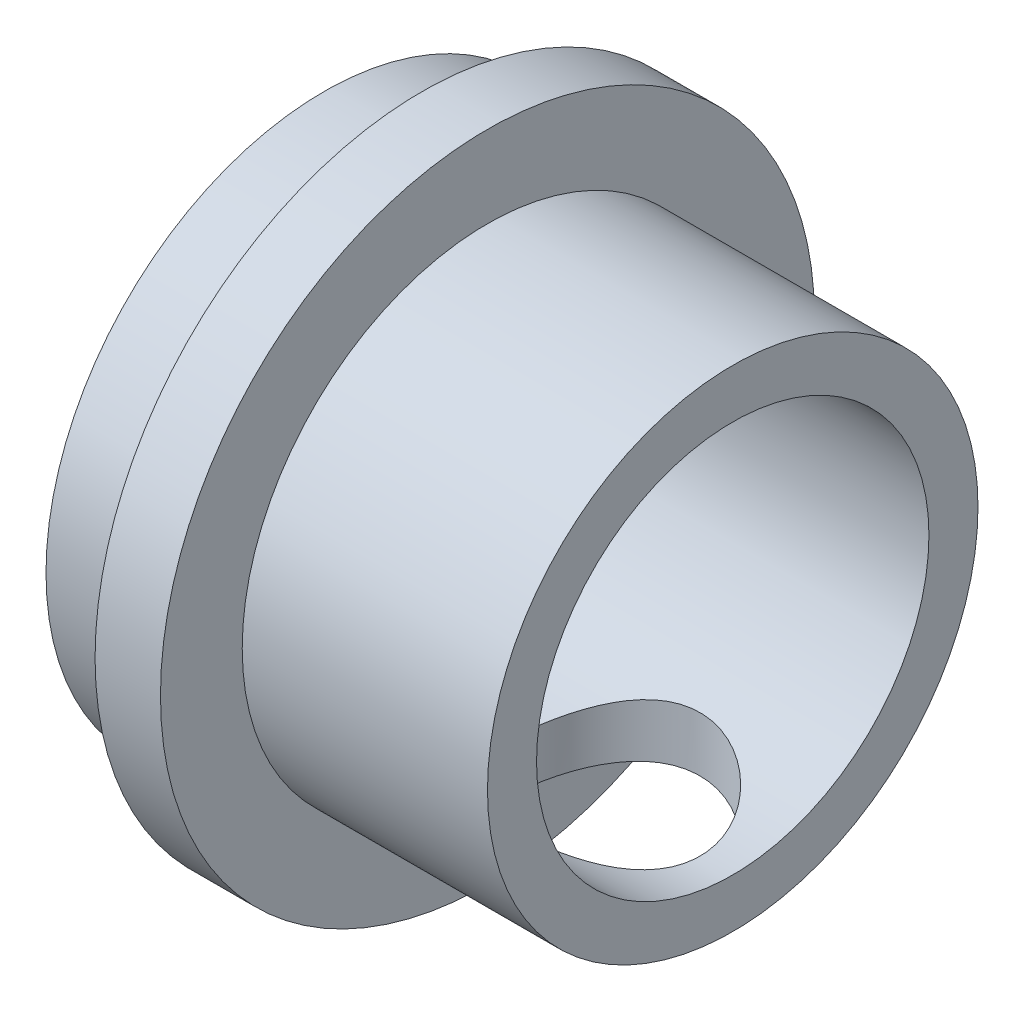
SolidWorks part; units mm, degrees
ref_plane "Face" through (0, 0, 0) normal (0, 0, 1) x (1, 0, 0)
ref_plane "Dessus" through (0, 0, 0) normal (0, 1, 0) x (1, 0, 0)
ref_plane "Droite" through (0, 0, 0) normal (1, 0, 0) x (0, 0, -1)
sketch "Esquisse1" plane through (0, 0, 0) normal (0, 0, 1) x (1, 0, 0)
  line L0 (-59.6035, 0) -> (58.8071, 0) construction
  line L1 (0, 0) -> (0, 8.5)
  line L2 (0, 8.5) -> (3, 8.5)
  line L3 (3, 8.5) -> (3, 9.0937)
  line L4 (3, 9.0937) -> (3, 10)
  line L5 (3, 10) -> (5, 10)
  line L6 (5, 10) -> (5, 7.5)
  line L7 (5, 7.5) -> (12.5, 7.5)
  line L8 (12.5, 7.5) -> (12.5, 0)
  line L9 (12.5, 0) -> (0, 0)
  dimension "D1" = 8.5
  dimension "D2" = 10
  dimension "D3" = 7.5
  dimension "D4" = 3
  dimension "D5" = 2
  dimension "D6" = 7.5
revolve "Révolution1" add sketch "Esquisse1" angle 360 about L0
sketch "Esquisse2" plane through (0, 0, 0) normal (-1, 0, 0) x (0, 0, 1)
  line L0 (-6.6668, 0) -> (7.051, 0) construction
  line L1 (0, 6.9357) -> (0, -4.6302) construction
  line L3 (-4, 4) -> (4, 4)
  line L4 (-4, 4) -> (-4, -4)
  line L5 (-4, -4) -> (4, -4)
  line L6 (4, 4) -> (4, -4)
  dimension "D1" = 8
  dimension "D2" = 8
extrude "Enlèv. mat.-Extru.1" cut sketch "Esquisse2" against normal through all
sketch "Esquisse3" plane through (12.5, 0, 0) normal (1, 0, 0) x (0, 0, -1)
  circle A0 centre (0, 0) radius 6
  dimension "D1" = 12
extrude "Enlèv. mat.-Extru.2" cut sketch "Esquisse3" against normal blind 10
sketch "Esquisse4" plane through (0, 0, 0) normal (0, 1, 0) x (1, 0, 0)
  line L0 (12.5, -7.5) -> (12.5, 7.5) construction
  line L2 (5, -7.5) -> (5, 7.5) construction
  circle A0 centre (8.5, 0) radius 3
  dimension "D1" = 6
  dimension "D2" = 4
  dimension "D3" = 3.5
extrude "Enlèv. mat.-Extru.3" cut sketch "Esquisse4" against normal blind 10
